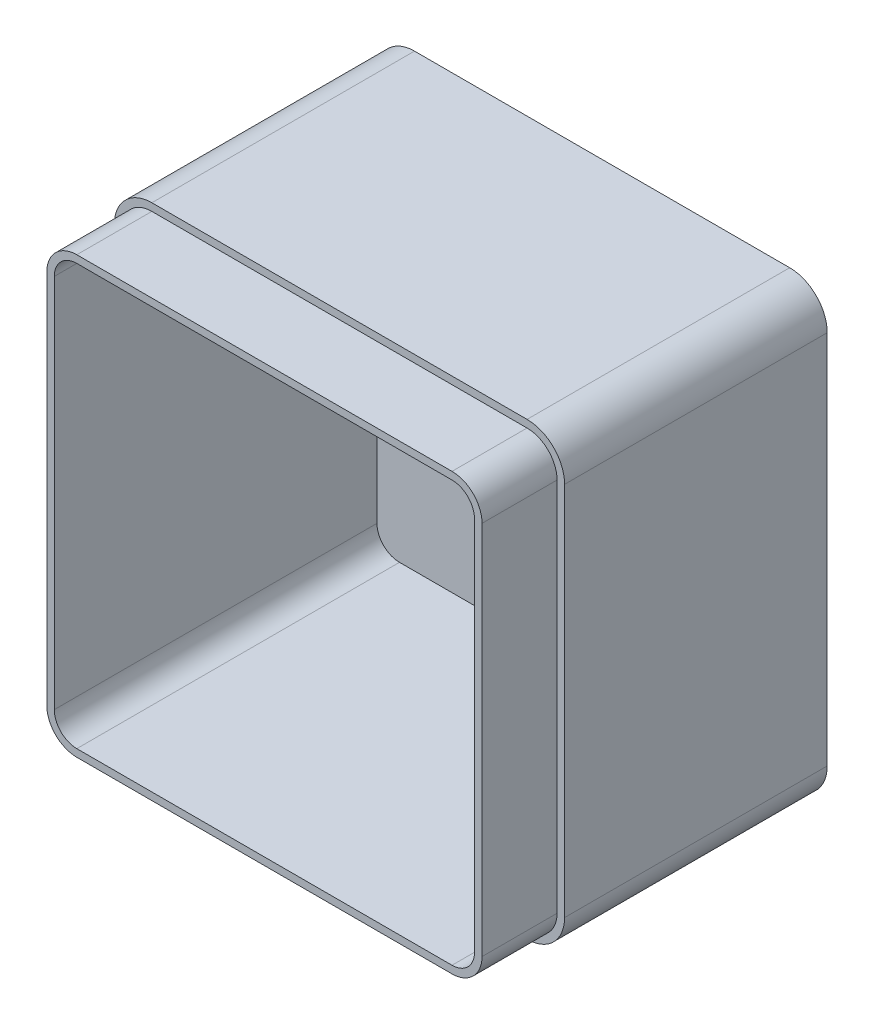
SolidWorks part; units mm, degrees
ref_plane "Front Plane" through (0, 0, 0) normal (0, 0, 1) x (1, 0, 0)
ref_plane "Top Plane" through (0, 0, 0) normal (0, 1, 0) x (1, 0, 0)
ref_plane "Right Plane" through (0, 0, 0) normal (1, 0, 0) x (0, 0, -1)
sketch "Sketch1" plane through (0, 0, 0) normal (0, 0, 1) x (1, 0, 0)
  line L1 (0, 0) -> (120, 0)
  line L2 (0, 0) -> (0, 120)
  line L3 (0, 120) -> (120, 120)
  line L4 (120, 0) -> (120, 120)
  dimension "D1" = 120
  dimension "D2" = 120
extrude "Boss-Extrude1" add sketch "Sketch1" along normal blind 90
fillet "Fillet1" radius 10 4 edges at (0, 0, 45) (120, 0, 45) (120, 120, 45) (0, 120, 45)
shell "Shell1" thickness 4
sketch "Sketch3" plane through (0, 0, 90) normal (0, 0, 1) x (1, 0, 0)
  line L0 (2, 110) -> (2, 10)
  line L1 (10, 2) -> (110, 2)
  line L2 (118, 10) -> (118, 110)
  line L3 (110, 118) -> (10, 118)
  line L4 (0, 110) -> (0, 10)
  line L5 (10, 0) -> (110, 0)
  line L6 (120, 10) -> (120, 110)
  line L7 (110, 120) -> (10, 120)
  line L8 (0, 110) -> (0, 10)
  line L9 (10, 0) -> (110, 0)
  line L10 (120, 10) -> (120, 110)
  line L11 (110, 120) -> (10, 120)
  arc A0 (2, 10) -> (10, 2) centre (10, 10) ccw
  arc A1 (110, 2) -> (118, 10) centre (110, 10) ccw
  arc A2 (118, 110) -> (110, 118) centre (110, 110) ccw
  arc A3 (10, 118) -> (2, 110) centre (10, 110) ccw
  arc A4 (0, 10) -> (10, 0) centre (10, 10) ccw
  arc A5 (110, 0) -> (120, 10) centre (110, 10) ccw
  arc A6 (120, 110) -> (110, 120) centre (110, 110) ccw
  arc A7 (10, 120) -> (0, 110) centre (10, 110) ccw
  arc A8 (0, 10) -> (10, 0) centre (10, 10) ccw
  arc A9 (110, 0) -> (120, 10) centre (110, 10) ccw
  arc A10 (120, 110) -> (110, 120) centre (110, 110) ccw
  arc A11 (10, 120) -> (0, 110) centre (10, 110) ccw
  dimension "D1" = 0
  dimension "D2" = 2
extrude "Cut-Extrude3" cut sketch "Sketch3" against normal blind 20
